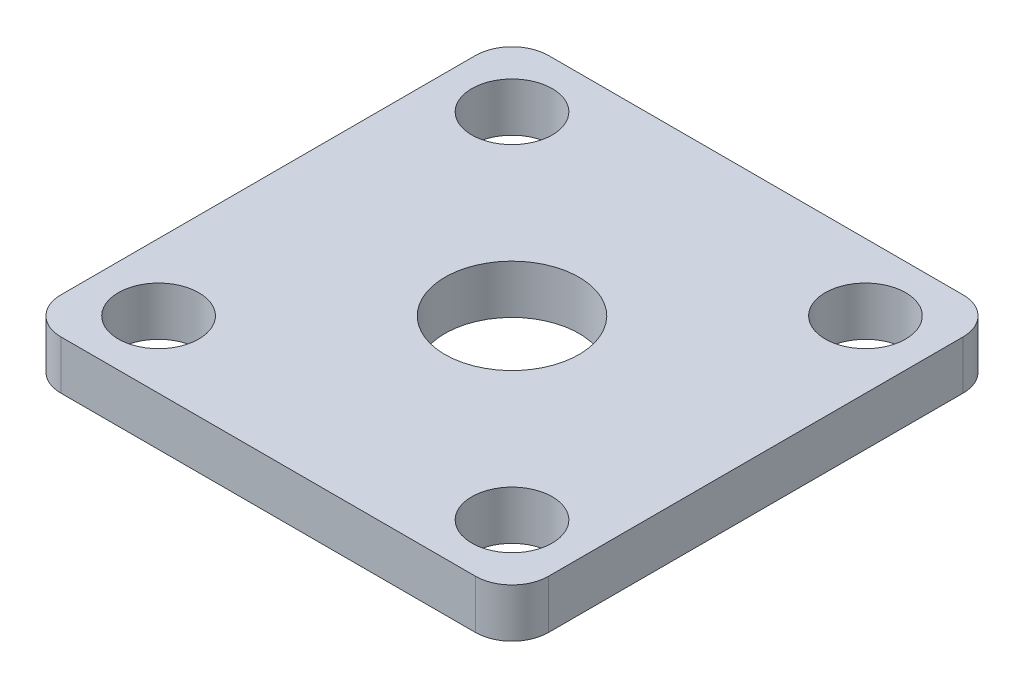
SolidWorks part; units mm, degrees
ref_plane "Спереди" through (0, 0, 0) normal (0, 0, 1) x (1, 0, 0)
ref_plane "Сверху" through (0, 0, 0) normal (0, 1, 0) x (1, 0, 0)
ref_plane "Справа" through (0, 0, 0) normal (1, 0, 0) x (0, 0, -1)
sketch "Эскиз1" plane through (0, 0, 0) normal (0, 1, 0) x (1, 0, 0)
  line L1 (-20, -20) -> (20, -20)
  line L2 (-20, -20) -> (-20, 20)
  line L3 (-20, 20) -> (20, 20)
  line L4 (20, -20) -> (20, 20)
  line L5 (-20, -20) -> (20, 20) construction
  line L6 (-20, 20) -> (20, -20) construction
  point P0 (0, 0)
  dimension "D1" = 40
  dimension "D2" = 40
extrude "Бобышка-Вытянуть1" add sketch "Эскиз1" along normal blind 4
hole_wizard "Отверстие с зазором M101" positions "Эскиз2" profile "Эскиз3" hole size "M10" standard "DIN" end condition through all
sketch "Эскиз2" plane through (0, 4, 0) normal (0, 1, 0) x (1, 0, 0)
  point P0 (0, 0)
sketch "Эскиз3" plane through (0, 4, 0) normal (1, 0, 0) x (0, 0, 1)
  line L0 (0, 0) -> (0, 4)
  line L1 (0, 4) -> (5.5, 4)
  line L2 (5.5, 4) -> (5.5, 0)
  line L5 (5.5, 0) -> (0, 0)
  line L11 (0, -6.35) -> (0, 107.95) construction
  dimension "Диаметр сквозного отверстия" = 11
  dimension "Глубина сквозного отверстия" = 4
fillet "Скругление1" radius 3 4 edges at (-20, 2, -20) (20, 2, -20) (-20, 2, 20) (20, 2, 20)
hole_wizard "Отверстие с зазором M61" positions "Эскиз4" profile "Эскиз5" hole size "M6" standard "DIN" end condition through all
sketch "Эскиз4" plane through (0, 0, 0) normal (0, -1, 0) x (-1, 0, 0)
  line L8 (-14.5, -14.5) -> (14.5, -14.5) construction
  line L9 (-14.5, -14.5) -> (-14.5, 14.5) construction
  line L10 (-14.5, 14.5) -> (14.5, 14.5) construction
  line L11 (14.5, -14.5) -> (14.5, 14.5) construction
  line L12 (-14.5, -14.5) -> (14.5, 14.5) construction
  line L13 (-14.5, 14.5) -> (14.5, -14.5) construction
  point P0 (-14.5, 14.5)
  point P19 (0, 0)
  point P20 (14.5, 14.5)
  point P93 (-14.5, -14.5)
  point P95 (14.5, -14.5)
  dimension "D1" = 29
sketch "Эскиз5" plane through (14.5, 0, -14.5) normal (1, 0, 0) x (0, 0, -1)
  line L0 (0, 0) -> (0, 4)
  line L1 (0, 4) -> (3.3, 4)
  line L2 (3.3, 4) -> (3.3, 0)
  line L5 (3.3, 0) -> (0, 0)
  line L11 (0, -6.35) -> (0, 107.95) construction
  dimension "Диаметр сквозного отверстия" = 6.6
  dimension "Глубина сквозного отверстия" = 4
